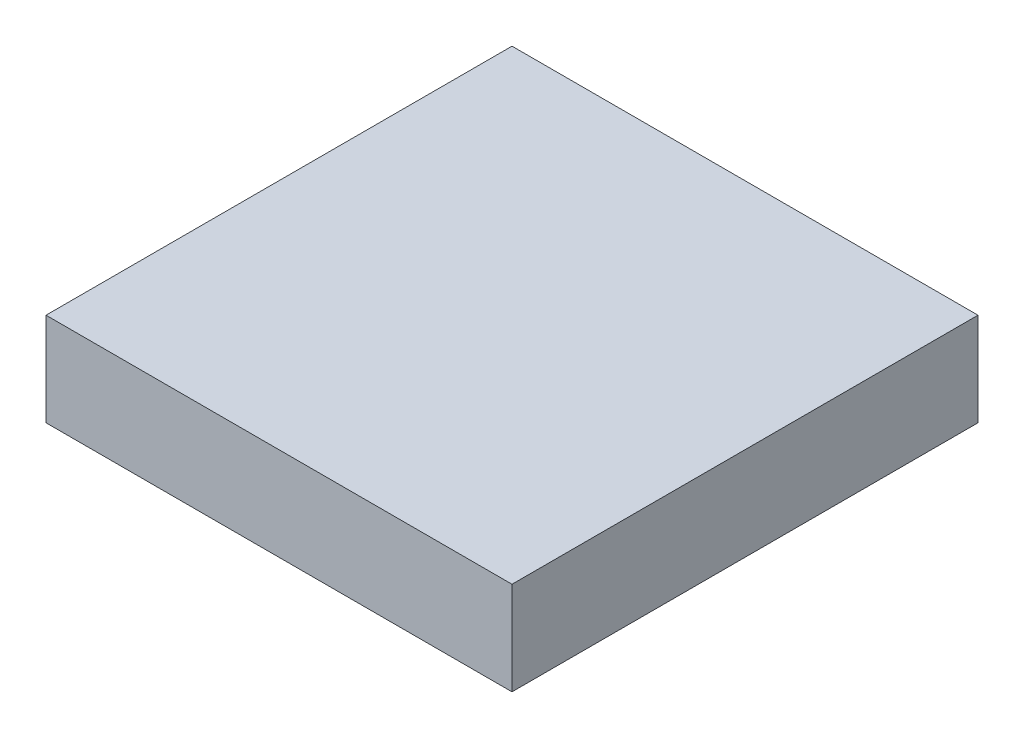
SolidWorks part; units mm, degrees
ref_plane "Front Plane" through (0, 0, 0) normal (0, 0, 1) x (1, 0, 0)
ref_plane "Top Plane" through (0, 0, 0) normal (0, 1, 0) x (1, 0, 0)
ref_plane "Right Plane" through (0, 0, 0) normal (1, 0, 0) x (0, 0, -1)
sketch "Sketch1" plane through (0, 0, 0) normal (0, 1, 0) x (1, 0, 0)
  line L1 (-7.5, -7.5) -> (7.5, -7.5)
  line L2 (-7.5, -7.5) -> (-7.5, 7.5)
  line L3 (-7.5, 7.5) -> (7.5, 7.5)
  line L4 (7.5, -7.5) -> (7.5, 7.5)
  line L5 (-7.5, -7.5) -> (7.5, 7.5) construction
  line L6 (-7.5, 7.5) -> (7.5, -7.5) construction
  point P0 (0, 0)
  dimension "D1" = 15
  dimension "D2" = 15
extrude "Boss-Extrude1" add sketch "Sketch1" along normal blind 3
sketch "Sketch2" plane through (0, 0, 0) normal (0, -1, 0) x (1, 0, 0)
  circle A0 centre (0, 0) radius 6
  circle A1 centre (0, 0) radius 2.5
  dimension "D1" = 12
  dimension "D2" = 5
extrude "Cut-Extrude1" cut sketch "Sketch2" against normal blind 2
sketch "Sketch3" plane through (0, 0, 0) normal (0, -1, 0) x (1, 0, 0)
  line L0 (-7.5, 7.5) -> (7.5, 7.5) construction
  line L1 (-7.5, -7.5) -> (-7.5, 7.5) construction
  line L2 (7.5, 7.5) -> (7.5, -7.5) construction
  line L3 (7.5, -7.5) -> (-7.5, -7.5) construction
  circle A0 centre (5.5, 5.5) radius 1.25
  circle A1 centre (-5.5, 5.5) radius 1.25
  circle A2 centre (-5.5, -5.5) radius 1.25
  circle A3 centre (5.5, -5.5) radius 1.25
  dimension "D1" = 2.5
  dimension "D4" = 2.5
  dimension "D7" = 2.5
  dimension "D10" = 2.5
  dimension "D2" = 2
  dimension "D3" = 2
  dimension "D5" = 2
  dimension "D6" = 2
  dimension "D8" = 2
  dimension "D9" = 2
  dimension "D11" = 2
  dimension "D12" = 2
extrude "Cut-Extrude2" cut sketch "Sketch3" against normal blind 2
